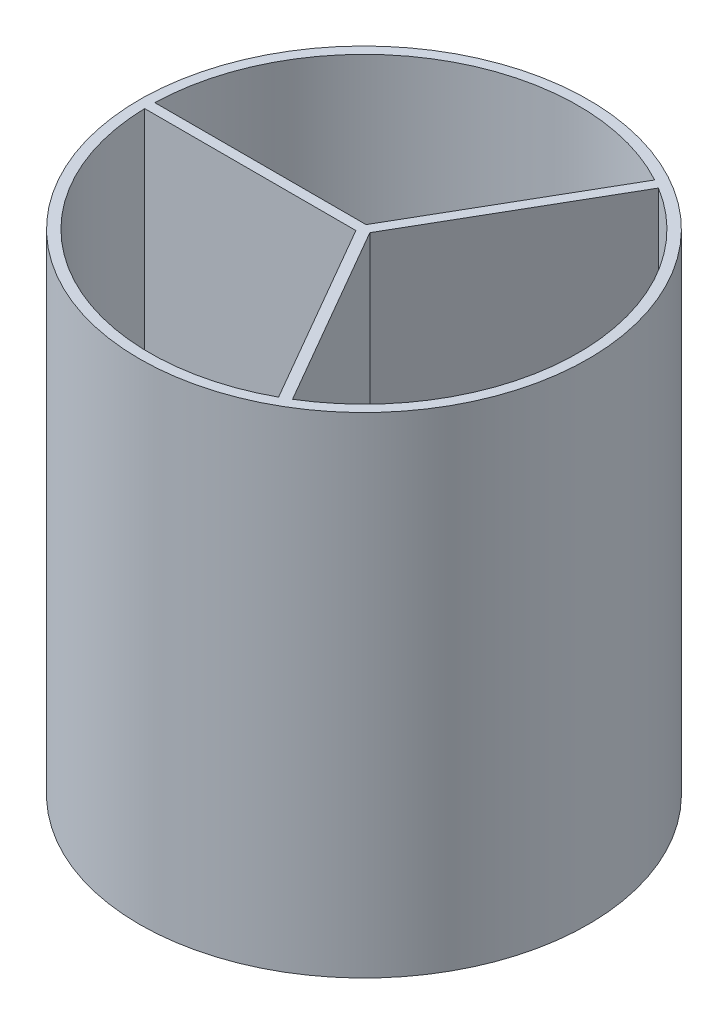
SolidWorks part; units mm, degrees
ref_plane "Front Plane" through (0, 0, 0) normal (0, 0, 1) x (1, 0, 0)
ref_plane "Top Plane" through (0, 0, 0) normal (0, 1, 0) x (1, 0, 0)
ref_plane "Right Plane" through (0, 0, 0) normal (1, 0, 0) x (0, 0, -1)
sketch "Sketch1" plane through (0, 0, 0) normal (0, 1, 0) x (1, 0, 0)
  circle A0 centre (0, 0) radius 279.4
  dimension "D1" = 558.8
extrude "Boss-Extrude1" add sketch "Sketch1" along normal blind 609.6 contours A0
sketch "Sketch3" plane through (0, 609.6, 0) normal (0, 1, 0) x (1, 0, 0)
  line L1 (-266.7, 6.3461) -> (1.3395, 6.3461)
  line L2 (-266.7, 6.3461) -> (-266.7, -6.3539)
  line L3 (-266.7, -6.3539) -> (1.3395, -6.3539)
  line L4 (1.3395, 6.3461) -> (1.3395, -6.3539)
  line L5 (-343.8781, 39.7118) -> (0, 27.0118) construction
  line L6 (-343.8781, 27.0118) -> (0, 39.7118) construction
  line L7 (138.8459, 227.7959) -> (127.8473, 234.1459)
  line L8 (138.8459, 227.7959) -> (4.8261, -4.333)
  line L9 (4.8261, -4.333) -> (-6.1724, 2.017)
  line L10 (127.8473, 234.1459) -> (-6.1724, 2.017)
  line L11 (127.8541, -234.142) -> (138.8527, -227.792)
  line L12 (127.8541, -234.142) -> (-6.1656, -2.013)
  line L13 (-6.1656, -2.013) -> (4.8329, 4.337)
  line L14 (138.8527, -227.792) -> (4.8329, 4.337)
  circle A0 centre (0, 0) radius 266.7
  circle A1 centre (0, 0) radius 279.4
  circle A2 centre (0, 0) radius 279.4
  point P5 (-171.9391, 33.3618)
  point P10 (0, 0)
  point P11 (0, 0)
  point P25 (0, 0)
  dimension "D3" = 12.7
  dimension "D4" = 3
  dimension "D1" = 0
  dimension "D2" = 12.7
extrude "Cut-Extrude1" cut sketch "Sketch3" against normal blind 596.9 contours L10 A0 L1 | L3 A0 L12 | L14 A0 L8
sketch "Sketch4" plane through (0, 0, 0) normal (0, -1, 0) x (1, 0, 0)
  circle A0 centre (0, 0) radius 12.7
extrude "Boss-Extrude2" add sketch "Sketch4" along normal blind 25.4
